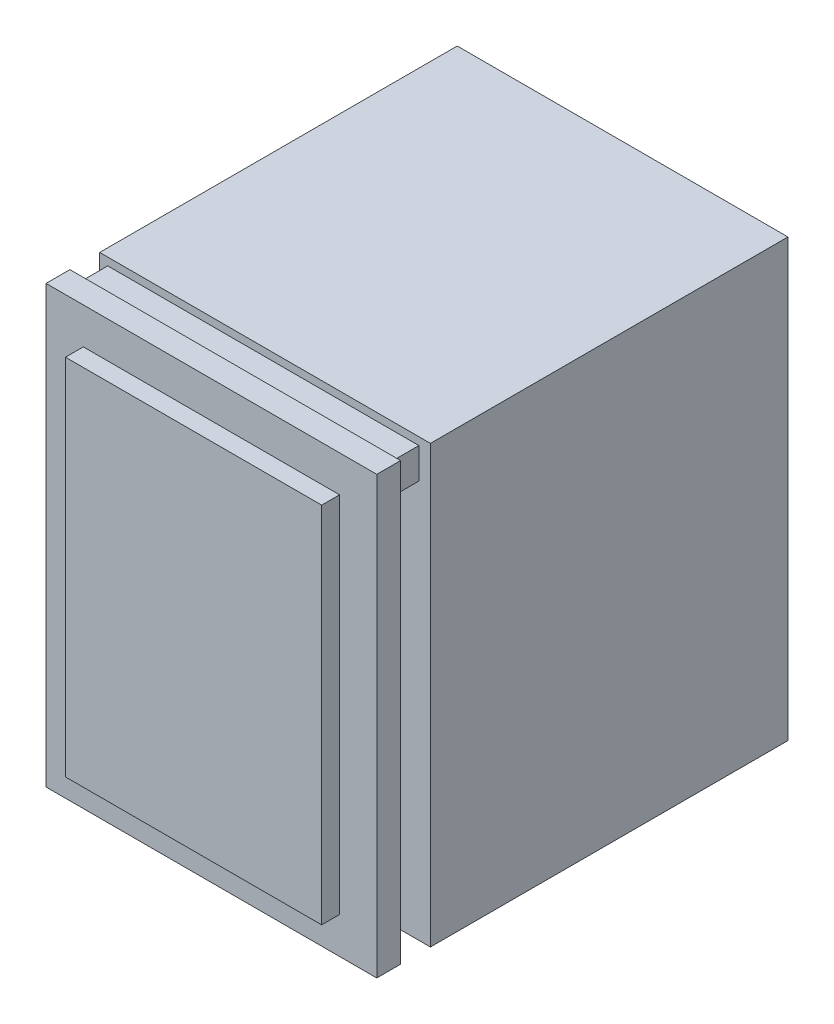
SolidWorks part; units mm, degrees
ref_plane "Front Plane" through (0, 0, 0) normal (0, 0, 1) x (1, 0, 0)
ref_plane "Top Plane" through (0, 0, 0) normal (0, 1, 0) x (1, 0, 0)
ref_plane "Right Plane" through (0, 0, 0) normal (1, 0, 0) x (0, 0, -1)
sketch "Sketch1" plane through (0, 0, 0) normal (0, 0, 1) x (1, 0, 0)
  line L1 (27.75, 36.6) -> (-27.75, 36.6)
  line L2 (27.75, 36.6) -> (27.75, -36.6)
  line L3 (27.75, -36.6) -> (-27.75, -36.6)
  line L4 (-27.75, 36.6) -> (-27.75, -36.6)
  line L5 (27.75, 36.6) -> (-27.75, -36.6) construction
  line L6 (27.75, -36.6) -> (-27.75, 36.6) construction
  point P0 (0, 0)
  dimension "D1" = 73.2
  dimension "D2" = 55.5
extrude "Boss-Extrude1" add sketch "Sketch1" along normal blind 4
sketch "Sketch2" plane through (0, 0, 0) normal (0, 0, -1) x (-1, 0, 0)
  line L1 (-25.8177, 35.3167) -> (26.4023, 35.3167)
  line L2 (-25.8177, 35.3167) -> (-25.8177, 30.1532)
  line L3 (-25.8177, 30.1532) -> (26.4023, 30.1532)
  line L4 (26.4023, 35.3167) -> (26.4023, 30.1532)
extrude "Boss-Extrude2" add sketch "Sketch2" along normal blind 5
sketch "Sketch3" plane through (0, 0, 4) normal (0, 0, 1) x (1, 0, 0)
  line L1 (21.5, 30.5) -> (-21.5, 30.5)
  line L2 (21.5, 30.5) -> (21.5, -30.5)
  line L3 (21.5, -30.5) -> (-21.5, -30.5)
  line L4 (-21.5, 30.5) -> (-21.5, -30.5)
  line L5 (21.5, 30.5) -> (-21.5, -30.5) construction
  line L6 (21.5, -30.5) -> (-21.5, 30.5) construction
  point P0 (0, 0)
  dimension "D1" = 43
  dimension "D2" = 61
extrude "Boss-Extrude3" add sketch "Sketch3" along normal blind 3
sketch "Sketch4" plane through (0, 0, -5) normal (0, 0, -1) x (-1, 0, 0)
  line L4 (27.75, -36.6) -> (27.75, 36.6)
  line L5 (27.75, 36.6) -> (-27.75, 36.6)
  line L6 (-27.75, 36.6) -> (-27.75, -36.6)
  line L7 (-27.75, -36.6) -> (27.75, -36.6)
  line L8 (27.75, -36.6) -> (27.75, 36.6)
  line L9 (27.75, 36.6) -> (-27.75, 36.6)
  line L10 (-27.75, 36.6) -> (-27.75, -36.6)
  line L11 (-27.75, -36.6) -> (27.75, -36.6)
  dimension "D1" = 0
extrude "Boss-Extrude4" add sketch "Sketch4" along normal blind 60
